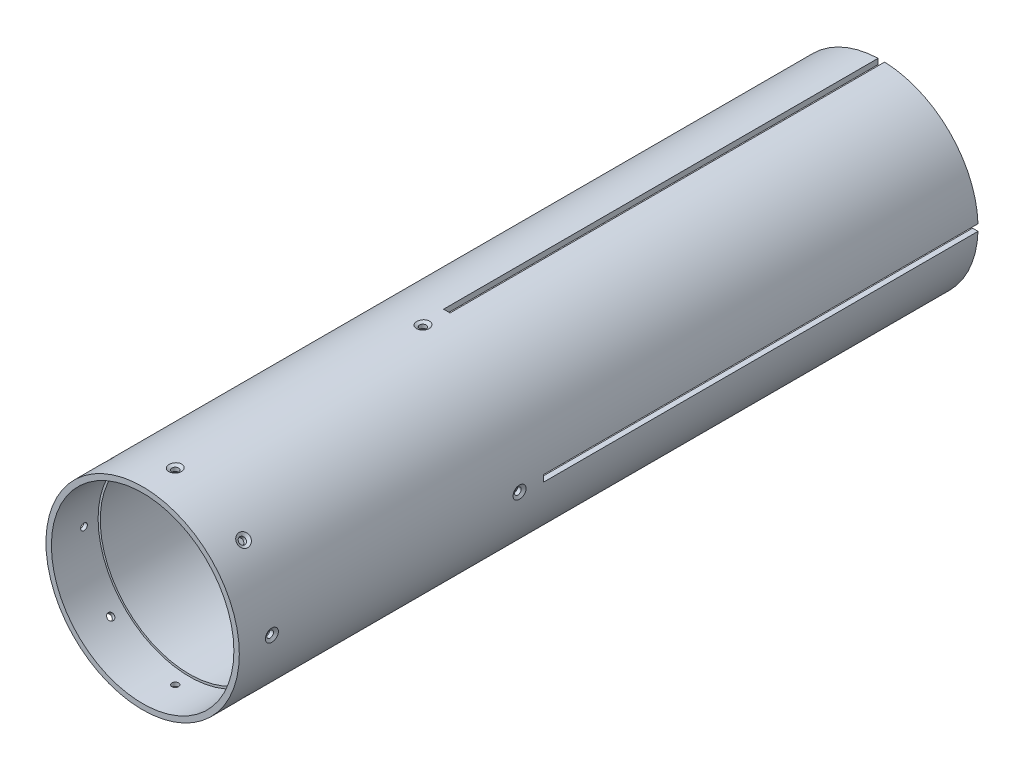
SolidWorks part; units mm, degrees
material "Hexcel AS4C (3000 Filaments)"
ref_plane "Plan de face" through (0, 0, 0) normal (0, 0, 1) x (1, 0, 0)
ref_plane "Plan de dessus" through (0, 0, 0) normal (0, 1, 0) x (1, 0, 0)
ref_plane "Plan de droite" through (0, 0, 0) normal (1, 0, 0) x (0, 0, -1)
sketch "Esquisse1" plane through (0, 0, 0) normal (0, 0, 1) x (1, 0, 0)
  circle A0 centre (0, 0) radius 44.5
  dimension "D1" = 89
extrude "Boss.-Extru.1" add sketch "Esquisse1" along normal blind 340
sketch "Esquisse2" plane through (0, 0, 0) normal (0, 0, -1) x (-1, 0, 0)
  circle A0 centre (0, 0) radius 42
  dimension "D1" = 84
extrude "Enlèv. mat.-Extru.1" cut sketch "Esquisse2" against normal blind 1150
sketch "Esquisse3" plane through (0, 0, 0) normal (0, 0, 1) x (1, 0, 0)
  line L0 (-12.1391, 0) -> (-67.8609, 0) construction
  line L1 (-50, 1.5) -> (-40, 1.5)
  line L2 (-50, 1.5) -> (-50, -1.5)
  line L3 (-50, -1.5) -> (-40, -1.5)
  line L4 (-40, 1.5) -> (-40, -1.5)
  point P8 (-40, 0)
  dimension "D1" = 3
  dimension "D2" = 10
  dimension "D3" = 40
extrude "Enlèv. mat.-Extru.2" cut sketch "Esquisse3" along normal blind 200
sketch "Esquisse4" plane through (0, 0, 0) normal (0, 0, -1) x (-1, 0, 0)
  line L0 (0, 0) -> (2.749, 0) construction
hole_wizard "Dégagement M2.51" positions "Esquisse3D1" profile "Esquisse5" hole size "M2.5" standard "ISO"
sketch3d "Esquisse3D1"
  line L7 (-44.5, 0, 0) -> (-44.5, 0, 422) construction
  line L8 (0, 0, 0) -> (-2.749, 0, 0) construction
  point P0 (-44.5, 0, 211)
  point P39 (-95.9154, -60.149, 0)
  dimension "D1" = 211
sketch "Esquisse5" plane through (-44.5, 0, 211) normal (0, 1, 0) x (0, 0, 1)
  line L0 (0, 0) -> (0, 15.9313)
  line L1 (0, 15.9313) -> (1.55, 15)
  line L2 (1.55, 15) -> (1.55, 0.8372)
  line L3 (1.55, 0.8372) -> (3, 0)
  line L5 (3, 0) -> (0, 0)
  line L6 (-1.55, 0.8372) -> (-3, 0) construction
  line L10 (0, 15.9313) -> (-1.55, 15) construction
  line L11 (0, -6.35) -> (0, 107.95) construction
  dimension "Diamètre du perçage" = 3.1
  dimension "Profondeur du perçage" = 15
  dimension "Diamètre du fraisage entrant" = 6
  dimension "Angle du fraisage entrant" = 120
  dimension "Angle de pointe" = 118
pattern_circular "Répétition circulaire1" count 4 over 360 about axis through (0, 0, 0) along (0, 0, 1) of "Dégagement M2.51", "Enlèv. mat.-Extru.2"
hole_wizard "Dégagement M2.52" positions "Esquisse3D2" profile "Esquisse6" hole size "M2.5" standard "ISO" end condition through all
sketch3d "Esquisse3D2"
  line L0 (0, 0, 340) -> (75.1527, 0, 340) construction
  line L1 (0, 0, 340) -> (0, 0, 200) construction
  line L4 (44.5, 0, 340) -> (44.5, 0, 325) construction
  point P0 (44.5, 0, 325)
  dimension "D1" = 15
sketch "Esquisse6" plane through (44.5, 0, 325) normal (0, 1, 0) x (0, 0, -1)
  line L0 (0, 0) -> (0, 107.4325)
  line L1 (0, 107.4325) -> (1.55, 107.4325)
  line L2 (1.55, 107.4325) -> (1.55, 0.8372)
  line L3 (1.55, 0.8372) -> (3, 0)
  line L5 (3, 0) -> (0, 0)
  line L6 (-1.55, 0.8372) -> (-3, 0) construction
  line L11 (0, -6.35) -> (0, 107.95) construction
  dimension "Diamètre du perçage jusqu'au prochain" = 3.1
  dimension "Profondeur du perçage jusqu'au prochain" = 107.4325
  dimension "Diamètre du fraisage entrant" = 6
  dimension "Angle du fraisage entrant" = 120
pattern_circular "Répétition circulaire2" count 8 over 360 about axis through (0, 0, 340) along (0, 0, 1) of "Dégagement M2.52"
sketch "Esquisse7" plane through (0, 0, 0) normal (0, 1, 0) x (1, 0, 0)
  line L0 (0, -353.0919) -> (0, 41.4176) construction
  line L1 (0, -340) -> (42, -340) construction
  line L2 (0, -318.5) -> (49.9974, -318.5) construction
  line L4 (42, -318.5) -> (42, -220) construction
  line L6 (42, -318.5) -> (41, -318.5)
  line L7 (0, -220) -> (67.2049, -220) construction
  line L8 (41, -318.5) -> (41, -220)
  line L9 (41, -220) -> (42, -220)
  line L10 (42, -220) -> (42, -318.5)
  dimension "D1" = 21.5
  dimension "D2" = 120
  dimension "D3" = 1
revolve "Révolution1" add sketch "Esquisse7" angle 360 about L0
